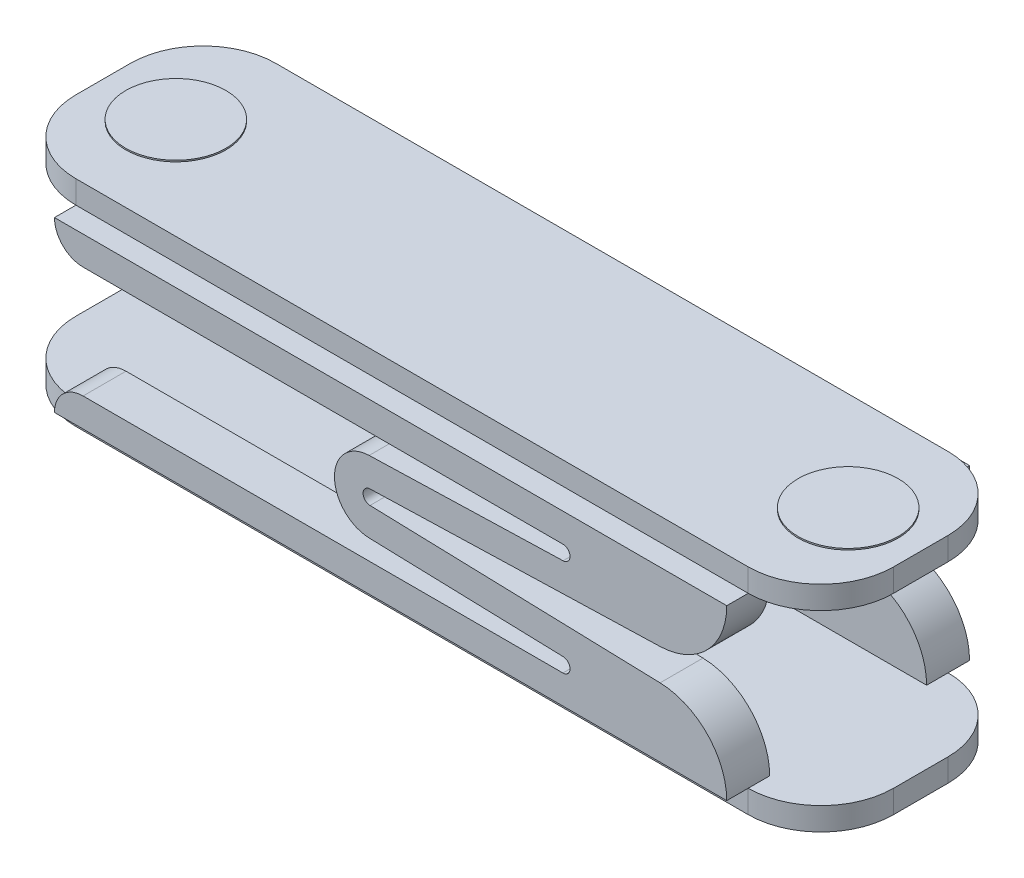
SolidWorks part; units mm, degrees
material "Acrylic (Medium-high impact)"
ref_plane "Front Plane" through (0, 0, 0) normal (0, 0, 1) x (1, 0, 0)
ref_plane "Top Plane" through (0, 0, 0) normal (0, 1, 0) x (1, 0, 0)
ref_plane "Right Plane" through (0, 0, 0) normal (1, 0, 0) x (0, 0, -1)
sketch "Sketch1" plane through (0, 0, 0) normal (0, 0, 1) x (1, 0, 0)
  line L1 (0, 0) -> (-57.15, 0)
  line L2 (0, 0) -> (0, 1.6)
  line L3 (0, 1.6) -> (-57.15, 1.6)
  line L4 (-57.15, 0) -> (-57.15, 1.6)
  line L5 (0, 15) -> (-57.15, 15)
  line L6 (0, 15) -> (0, 13.4)
  line L7 (0, 13.4) -> (-57.15, 13.4)
  line L8 (-57.15, 15) -> (-57.15, 13.4)
  dimension "D1" = 57.15
  dimension "D2" = 1.6
  dimension "D3" = 15
extrude "Boss-Extrude1" add sketch "Sketch1" along normal blind 13.97
fillet "Fillet1" radius 5.08 4 edges at (0, 14.2, 13.97) (0, 14.2, 0) (-57.15, 14.2, 13.97) (-57.15, 14.2, 0)
fillet "Fillet2" radius 5.08 4 edges at (0, 0.8, 13.97) (-57.15, 0.8, 13.97) (-57.15, 0.8, 0) (0, 0.8, 0)
sketch "Sketch2" plane through (0, 0, 13.97) normal (0, 0, 1) x (1, 0, 0)
  line L0 (-30.0148, 7.9998) -> (-9.74, 8.6)
  line L1 (-5.08, 13.4) -> (-52.07, 13.4)
  line L3 (-50.07, 11.4) -> (-16.5328, 11.4)
  line L4 (-16.518, 10.4002) -> (-30.074, 9.9989)
  line L5 (-57.15, 13.4) -> (-57.15, 1.6) construction
  line L6 (-57.15, 13.4) -> (-52.07, 13.4) construction
  line L7 (-57.15, 1.6) -> (-57.15, 7.5) construction
  line L8 (-57.15, 7.5) -> (0, 7.5) construction
  line L10 (-52.07, 13.4) -> (-5.08, 13.4) construction
  line L11 (-16.518, 4.5998) -> (-30.074, 5.0011)
  line L12 (-30.0148, 7.0002) -> (-9.74, 6.4)
  line L13 (-5.08, 1.6) -> (-52.07, 1.6)
  line L14 (-50.07, 3.6) -> (-16.5328, 3.6)
  arc A0 (-30.074, 9.9989) -> (-30.074, 5.0011) centre (-30, 7.5) ccw
  arc A1 (-30.0148, 7.9998) -> (-30.0148, 7.0002) centre (-30, 7.5) ccw
  arc A2 (-16.5328, 11.4) -> (-16.518, 10.4002) centre (-16.5328, 10.9) cw
  arc A3 (-9.74, 8.6) -> (-5.08, 13.4) centre (-9.8821, 13.4) ccw
  arc A4 (-52.07, 13.4) -> (-50.07, 11.4) centre (-50.07, 13.4) ccw
  arc A5 (-16.5328, 3.6) -> (-16.518, 4.5998) centre (-16.5328, 4.1) ccw
  arc A6 (-9.74, 6.4) -> (-5.08, 1.6) centre (-9.8821, 1.6) cw
  arc A7 (-52.07, 1.6) -> (-50.07, 3.6) centre (-50.07, 1.6) cw
  point P1 (-52.07, 13.4)
  point P34 (-9.5649, 8.7964)
  point P35 (-38, 7.9998)
  point P38 (-7.1551, 3.8907)
  point P39 (-38.0545, 7.5)
  point P40 (0, 0)
  point P41 (0, 0)
  point P42 (-42.5658, 5.8069)
  point P43 (0, 0)
  dimension "D1" = 0.5
  dimension "D4" = 30
  dimension "D2" = 2
  dimension "D3" = 2
  dimension "D5" = 2.2
extrude "Boss-Extrude3" add sketch "Sketch2" against normal mid plane 3
ref_plane "Plane1" through (0, 0, 6.985) normal (0, 0, -1) x (-1, 0, 0)
mirror "Mirror2" about plane through (0, 0, 6.985) normal (0, 0, -1) of "Boss-Extrude3"
sketch "Sketch3" plane through (0, 15, 0) normal (0, 1, 0) x (1, 0, 0)
  line L0 (-52.07, 0) -> (-52.07, -13.97) construction
  line L1 (-5.08, 0) -> (-5.08, -13.97) construction
  line L2 (-57.15, -8.89) -> (-57.15, -5.08) construction
  line L3 (-57.15, -6.985) -> (0, -6.985) construction
  line L4 (0, -8.89) -> (0, -5.08) construction
  line L5 (-5.08, -13.97) -> (-52.07, -13.97) construction
  line L6 (-52.07, -13.97) -> (-5.08, -13.97) construction
  circle A0 centre (-52.07, -6.985) radius 3.5
  circle A1 centre (-5.08, -6.985) radius 3.5
  dimension "D1" = 7
extrude "Boss-Extrude4" add sketch "Sketch3" along normal blind 0.1 contours A1 | A0
ref_plane "Plane2" through (0, 7.5, 0) normal (0, 1, 0) x (1, 0, 0)
mirror "Mirror3" about plane through (0, 7.5, 0) normal (0, 1, 0) of "Boss-Extrude4"
equation "\"D1@Sketch2\"= 1/ \"D3@Sketch2\""
